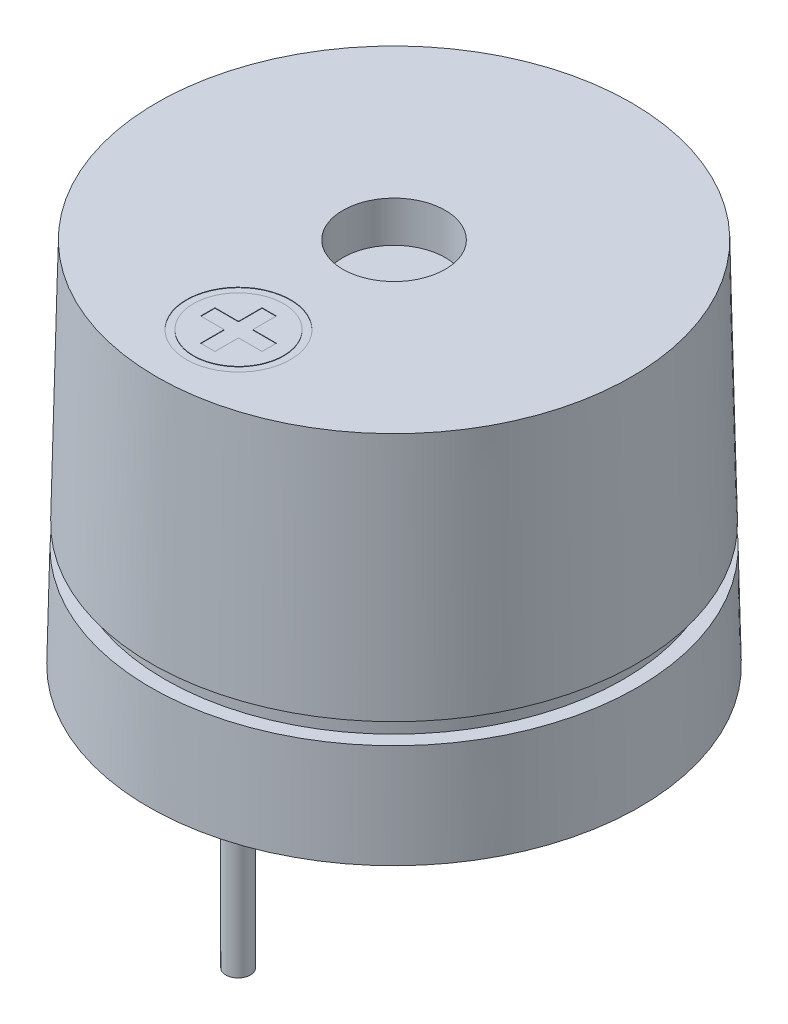
SolidWorks part; units mm, degrees
material "ABS"
ref_plane "Front Plane" through (0, 0, 0) normal (0, 0, 1) x (1, 0, 0)
ref_plane "Top Plane" through (0, 0, 0) normal (0, 1, 0) x (1, 0, 0)
ref_plane "Right Plane" through (0, 0, 0) normal (1, 0, 0) x (0, 0, -1)
sketch "Sketch1" plane through (0, 0, 0) normal (0, 0, 1) x (1, 0, 0)
  line L0 (0, 0) -> (0, 9)
  line L1 (0, 0) -> (6, 0)
  line L2 (6, 0) -> (5.8, 9)
  line L3 (5.8, 9) -> (0, 9)
  dimension "D1" = 6
  dimension "D2" = 9
  dimension "D3" = 5.8
revolve "Revolve1" add sketch "Sketch1" angle 360 about L0
sketch "Sketch2" plane through (0, 0, 0) normal (0, -1, 0) x (1, 0, 0)
  line L0 (0, 0) -> (0, 5.4) construction
  line L1 (0, 5.4) -> (0, 6) construction
  circle A0 centre (0, 0) radius 5.4
  circle A1 centre (0, 0) radius 6 construction
  dimension "D1" = 0.6
extrude "Cut-Extrude1" cut sketch "Sketch2" against normal blind 0.5
sketch "Sketch4" plane through (0, 0.5, 0) normal (0, -1, 0) x (1, 0, 0)
  line L0 (0, 3.81) -> (0, -3.81) construction
  circle A0 centre (0, -3.81) radius 0.3
  circle A1 centre (0, 3.81) radius 0.3
  dimension "D2" = 0.6
  dimension "D1" = 7.62
extrude "Boss-Extrude2" add sketch "Sketch4" along normal blind 5
sketch "Sketch5" plane through (0, 9, 0) normal (0, 1, 0) x (1, 0, 0)
  line L0 (0, 0) -> (0, -3.8) construction
  circle A0 centre (0, -3.8) radius 1.27
  circle A1 centre (0, -3.8) radius 1.1
  dimension "D1" = 2.54
  dimension "D2" = 2.2
  dimension "D3" = 3.8
extrude "Cut-Extrude2" cut sketch "Sketch5" against normal blind 0.01
sketch "Sketch6" plane through (0, 9, 0) normal (0, 1, 0) x (1, 0, 0)
  line L0 (-1.1, -3.8) -> (-0.75, -3.8) construction
  line L1 (1.1, -3.8) -> (0.75, -3.8) construction
  line L2 (0.75, -3.8) -> (0, -3.8) construction
  line L3 (0, -3.8) -> (-0.75, -3.8) construction
  line L4 (0, -3.8) -> (0, -3.05) construction
  line L5 (0, -3.05) -> (0, -2.7) construction
  line L6 (0, -3.8) -> (0, -4.55) construction
  line L7 (0, -4.55) -> (0, -4.9) construction
  line L8 (-0.175, -3.05) -> (0.175, -3.05)
  line L9 (-0.175, -4.55) -> (0.175, -4.55)
  line L10 (0.75, -3.625) -> (0.75, -3.975)
  line L11 (-0.75, -3.625) -> (-0.75, -3.975)
  line L12 (-0.75, -3.625) -> (-0.175, -3.625)
  line L13 (-0.175, -3.625) -> (-0.175, -3.05)
  line L14 (0.175, -3.05) -> (0.175, -3.625)
  line L15 (0.175, -3.625) -> (0.75, -3.625)
  line L16 (0.75, -3.975) -> (0.175, -3.975)
  line L17 (0.175, -3.975) -> (0.175, -4.55)
  line L18 (-0.75, -3.975) -> (-0.175, -3.975)
  line L19 (-0.175, -3.975) -> (-0.175, -4.55)
  line L20 (-0.175, -3.975) -> (-0.175, -3.625) construction
  line L21 (-0.175, -3.625) -> (0.175, -3.625) construction
  line L22 (0.175, -3.625) -> (0.175, -3.975) construction
  line L23 (0.175, -3.975) -> (-0.175, -3.975) construction
  circle A0 centre (0, -3.8) radius 1.1 construction
  circle A1 centre (0, -3.8) radius 1.1 construction
  dimension "D1" = 0.35
  dimension "D2" = 1.5
extrude "Cut-Extrude3" cut sketch "Sketch6" against normal blind 0.01
sketch "Sketch7" plane through (0, 9, 0) normal (0, 1, 0) x (1, 0, 0)
  circle A0 centre (0, 0) radius 1.25
  dimension "D1" = 2.5
extrude "Cut-Extrude4" cut sketch "Sketch7" against normal blind 3
sketch "Sketch8" plane through (0, 6, 0) normal (0, 1, 0) x (1, 0, 0)
  circle A0 centre (0, 0) radius 4.5
  dimension "D1" = 9
extrude "Cut-Extrude5" cut sketch "Sketch8" along normal blind 2
sketch "Sketch12" plane through (0, 0.5, 0) normal (0, -1, 0) x (1, 0, 0)
  circle A0 centre (0, 3.81) radius 1.25
  circle A1 centre (0, -3.81) radius 1.25
  dimension "D1" = 2.5
extrude "Boss-Extrude4" add sketch "Sketch12" along normal blind 0.5 draft 45
fillet "Fillet3" radius 1 2 edges at (0, 0, 3.06) (0, 0, -4.56)
sketch "Sketch13" plane through (0, 0, 0) normal (0, 0, 1) x (1, 0, 0)
  line L0 (0, 0) -> (0, 2.75) construction
  line L1 (-0.3, 0) -> (0.3, 0) construction
  line L2 (0, 2.75) -> (5.6, 2.75) construction
  line L3 (5.6, 2.75) -> (6.6, 2.75) construction
  line L4 (5.6, 3) -> (6.6, 3)
  line L5 (5.6, 3) -> (5.6, 2.5)
  line L6 (5.6, 2.5) -> (6.6, 2.5)
  line L7 (6.6, 3) -> (6.6, 2.5)
  dimension "D1" = 2.75
  dimension "D2" = 0.5
  dimension "D3" = 5.6
  dimension "D4" = 1
revolve "Cut-Revolve1" cut sketch "Sketch13" angle 360 about L0
